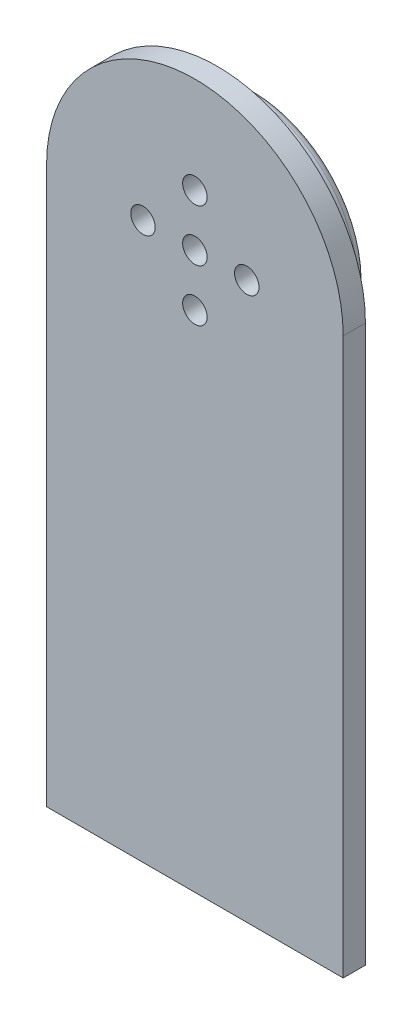
SolidWorks part; units mm, degrees
ref_plane "前视基准面" through (0, 0, 0) normal (0, 0, 1) x (1, 0, 0)
ref_plane "上视基准面" through (0, 0, 0) normal (0, 1, 0) x (1, 0, 0)
ref_plane "右视基准面" through (0, 0, 0) normal (1, 0, 0) x (0, 0, -1)
sketch "草图1" plane through (0, 0, 0) normal (0, 0, 1) x (1, 0, 0)
  circle A0 centre (0, 0) radius 1.65
  circle A1 centre (0, 7) radius 1.65
  circle A2 centre (7, 0) radius 1.65
  circle A3 centre (0, -7) radius 1.65
  circle A4 centre (-7, 0) radius 1.65
  circle A5 centre (0, 0) radius 15
  point P14 (0, 0)
  dimension "D1" = 3.3
  dimension "D2" = 3.3
  dimension "D5" = 30
  dimension "D3" = 7
  dimension "D4" = 4
extrude "凸台-拉伸1" add sketch "草图1" along normal blind 8
fillet "圆角1" radius 1 1 edges at (15, 0, 0)
sketch "草图2" plane through (0, 0, 8) normal (0, 0, 1) x (1, 0, 0)
  line L1 (-20, 0) -> (20, 0)
  line L2 (-20, 0) -> (-20, -75)
  line L3 (-20, -75) -> (20, -75)
  line L4 (20, 0) -> (20, -75)
  circle A0 centre (0, 0) radius 20
  circle A1 centre (0, 0) radius 15
  circle A2 centre (0, 0) radius 15
  circle M8 centre (0, 0) radius 15
  dimension "D2" = 40
  dimension "D3" = 75
  dimension "D1" = 0
extrude "凸台-拉伸2" add sketch "草图2" against normal blind 3 contours L1 A0 M8 | L1 A0 M8 | A0 L2 L3 L4
